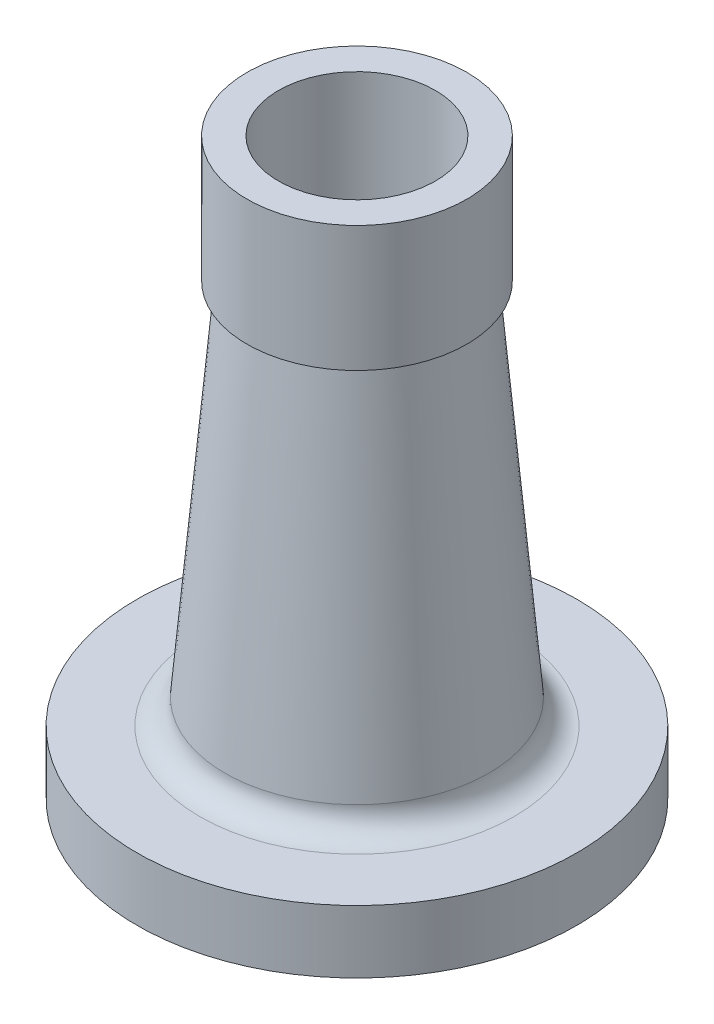
SolidWorks part; units mm, degrees
ref_plane "Front Plane" through (0, 0, 0) normal (0, 0, 1) x (1, 0, 0)
ref_plane "Top Plane" through (0, 0, 0) normal (0, 1, 0) x (1, 0, 0)
ref_plane "Right Plane" through (0, 0, 0) normal (1, 0, 0) x (0, 0, -1)
sketch "Sketch1" plane through (0, 0, 0) normal (0, 0, 1) x (1, 0, 0)
  line L0 (0, -90.2789) -> (0, 92.5) construction
  line L1 (29.0626, -28.9988) -> (35, -87.2789)
  line L2 (29.0626, -28.9988) -> (25, 17.342)
  line L3 (25, 92.5) -> (35, 92.5)
  line L4 (35, 92.5) -> (35, 52.5)
  line L5 (50, -90.2789) -> (70, -90.2789)
  line L6 (70, -90.2789) -> (70, -70.2789)
  line L7 (70, -70.2789) -> (50, -70.2789)
  line L9 (35, 52.5) -> (32, 52.5)
  line L10 (32, 52.5) -> (42, -62.2789)
  line L11 (35, -87.2789) -> (50, -87.2789)
  line L12 (50, -87.2789) -> (50, -90.2789)
  line L13 (25, 92.5) -> (25, 17.342)
  arc A0 (42, -62.2789) -> (50, -70.2789) centre (50, -62.2789) ccw
  dimension "D5" = 70
  dimension "D1" = 0
  dimension "D2" = 92.5
revolve "Revolve1" add sketch "Sketch1" angle 360 about L0
fillet "Fillet1" radius 1.5 1 edges at (0, -87.2789, -50)
